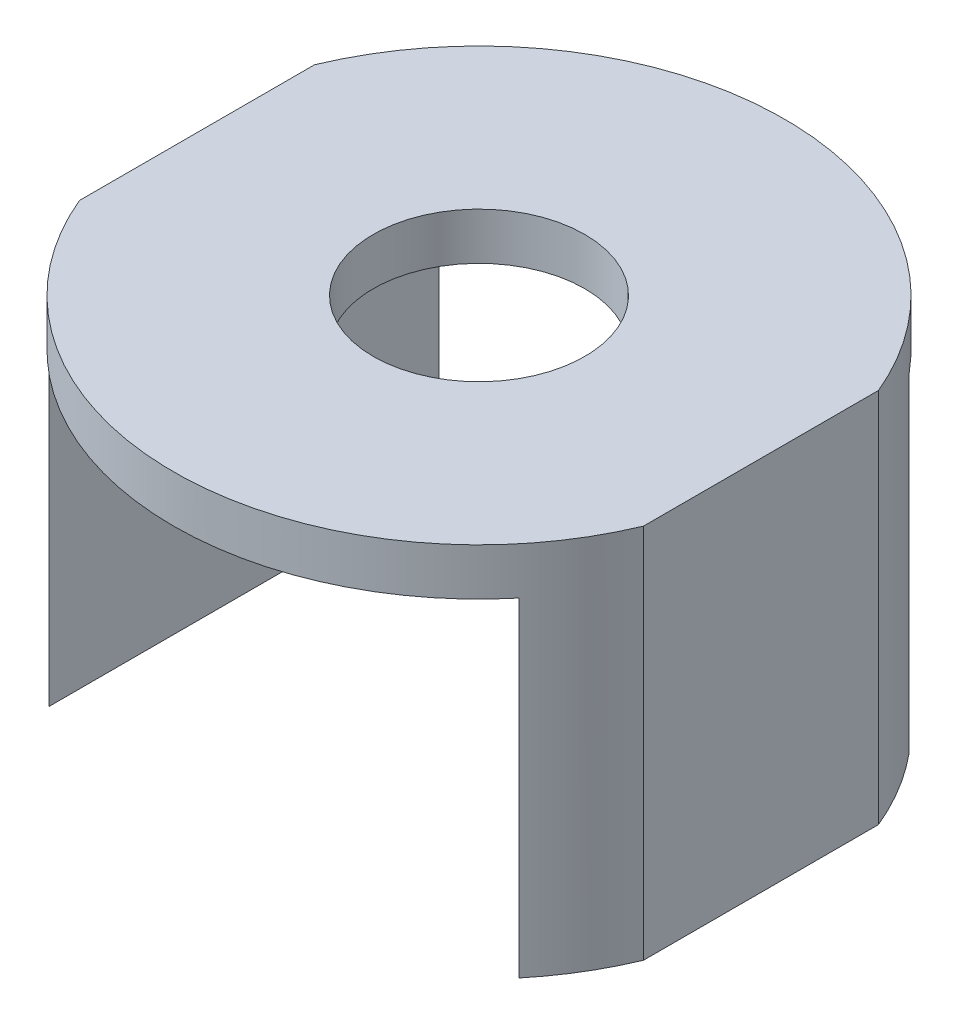
SolidWorks part; units mm, degrees
ref_plane "Front Plane" through (0, 0, 0) normal (0, 0, 1) x (1, 0, 0)
ref_plane "Top Plane" through (0, 0, 0) normal (0, 1, 0) x (1, 0, 0)
ref_plane "Right Plane" through (0, 0, 0) normal (1, 0, 0) x (0, 0, -1)
sketch "Sketch1" plane through (0, 0, 0) normal (0, 0, 1) x (1, 0, 0)
  line L1 (-38.1, 25.4) -> (38.1, 25.4)
  line L2 (-38.1, 25.4) -> (-38.1, -25.4)
  line L3 (-38.1, -25.4) -> (38.1, -25.4)
  line L4 (38.1, 25.4) -> (38.1, -25.4)
  line L5 (-38.1, 25.4) -> (38.1, -25.4) construction
  line L6 (-38.1, -25.4) -> (38.1, 25.4) construction
  line L7 (-31.75, 19.05) -> (31.75, 19.05)
  line L8 (-31.75, 19.05) -> (-31.75, -19.05)
  line L9 (-31.75, -19.05) -> (31.75, -19.05)
  line L10 (31.75, 19.05) -> (31.75, -19.05)
  line L11 (-31.75, 19.05) -> (31.75, -19.05) construction
  line L12 (-31.75, -19.05) -> (31.75, 19.05) construction
  point P0 (0, 0)
  point P5 (0, 0)
  dimension "D1" = 50.8
  dimension "D2" = 76.2
  dimension "D3" = 6.35
  dimension "D4" = 6.35
extrude "Boss-Extrude1" add sketch "Sketch1" along normal blind 114.3
sketch "Sketch2" plane through (0, 25.4, 0) normal (0, 1, 0) x (1, 0, 0)
  line L0 (0, 0) -> (0, -114.3) construction
  line L1 (38.1, 0) -> (-38.1, 0) construction
  line L2 (38.1, -114.3) -> (-38.1, -114.3) construction
  line L3 (38.1, -57.15) -> (-38.1, -57.15) construction
  line L4 (38.1, -114.3) -> (38.1, 0) construction
  line L5 (-38.1, -114.3) -> (-38.1, 0) construction
  circle A0 centre (0, -57.15) radius 41.275
  circle A1 centre (0, -57.15) radius 14.2875
  line M1 (38.1, 0) -> (-38.1, 0)
  line M2 (-38.1, 0) -> (-38.1, -114.3)
  line M3 (-38.1, -114.3) -> (38.1, -114.3)
  line M4 (38.1, -114.3) -> (38.1, 0)
  dimension "D1" = 82.55
  dimension "D2" = 28.575
extrude "Cut-Extrude2" cut sketch "Sketch2" against normal blind 114.3 contours A0 M2 M3 M4 | A1 | A0 M4 M1 M2
sketch "Sketch3" plane through (0, -25.4, 0) normal (0, -1, 0) x (1, 0, 0)
  line L1 (-31.75, 6.35) -> (31.75, 6.35)
  line L2 (-31.75, 6.35) -> (-31.75, 107.95)
  line L3 (-31.75, 107.95) -> (31.75, 107.95)
  line L4 (31.75, 6.35) -> (31.75, 107.95)
  line L5 (-31.75, 6.35) -> (31.75, 107.95) construction
  line L6 (-31.75, 107.95) -> (31.75, 6.35) construction
  point P0 (0, 57.15)
  dimension "D1" = 101.6
  dimension "D2" = 63.5
extrude "Cut-Extrude3" cut sketch "Sketch3" against normal blind 7.62
